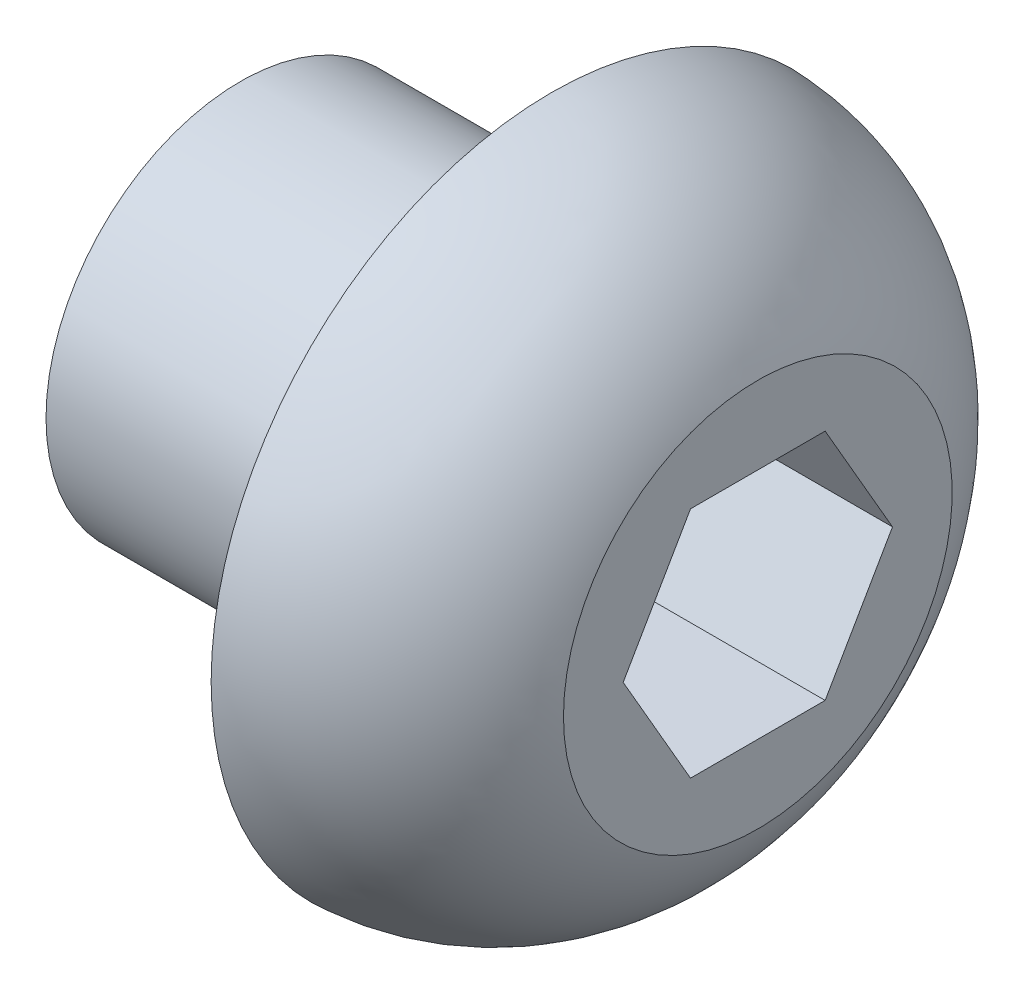
SolidWorks part; units mm, degrees
ref_plane "Front" through (0, 0, 0) normal (0, 0, 1) x (1, 0, 0)
ref_plane "Top" through (0, 0, 0) normal (0, 1, 0) x (1, 0, 0)
ref_plane "Right" through (0, 0, 0) normal (1, 0, 0) x (0, 0, -1)
sketch "Sketch1" plane through (0, 0, 0) normal (0, 0, 1) x (1, 0, 0)
  line L0 (-7.1096, 0) -> (25.0745, 0) construction
  line L1 (0, 0) -> (0, 3.9688)
  line L2 (0, 3.9688) -> (6.35, 3.9688)
  line L3 (6.35, 3.9688) -> (6.35, 6.9469)
  line L4 (0, 0) -> (10.5664, 0)
  line L5 (10.5664, 0) -> (10.5664, 3.9688)
  arc A0 (6.35, 6.9469) -> (10.5664, 3.9688) centre (6.1295, 2.1609) cw
  dimension "D1" = 6.9469
  dimension "SCREW DIAMETER" = 7.9375
  dimension "HEAD THICKNESS" = 4.2164
  dimension "SCREW LENGTH" = 6.35
revolve "Base-Revolve" add sketch "Sketch1" angle 360 about L0
sketch "Sketch2" plane through (10.5664, 0, 0) normal (1, 0, 0) x (0, 0, -1)
  line L1 (2.7496, 0) -> (1.3748, 2.3813)
  line L2 (1.3748, 2.3813) -> (-1.3748, 2.3813)
  line L3 (-1.3748, 2.3813) -> (-2.7496, 0)
  line L4 (-2.7496, 0) -> (-1.3748, -2.3812)
  line L5 (-1.3748, -2.3812) -> (1.3748, -2.3813)
  line L6 (1.3748, -2.3813) -> (2.7496, 0)
  circle A0 centre (0, 0) radius 2.3813 construction
  dimension "HEX DIMENSION" = 4.7625
extrude "HEX" cut sketch "Sketch2" against normal blind 3.81
